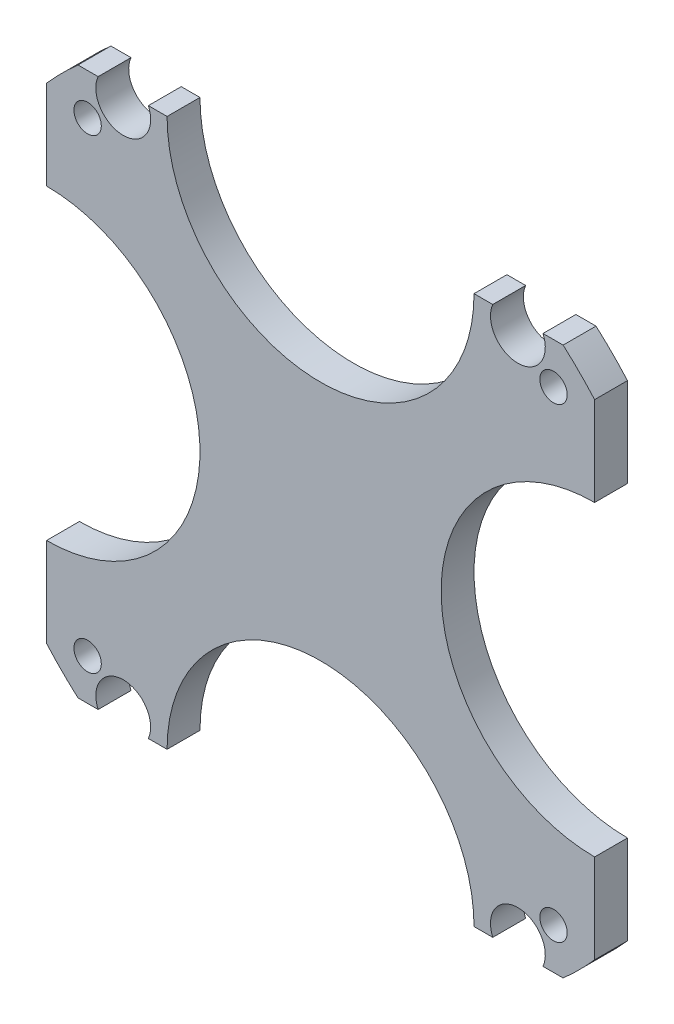
SolidWorks part; units mm, degrees
ref_plane "前视基准面" through (0, 0, 0) normal (0, 0, 1) x (1, 0, 0)
ref_plane "上视基准面" through (0, 0, 0) normal (0, 1, 0) x (1, 0, 0)
ref_plane "右视基准面" through (0, 0, 0) normal (1, 0, 0) x (0, 0, -1)
sketch "草图1" plane through (0, 0, 0) normal (0, 0, 1) x (1, 0, 0)
  line L0 (55, 0) -> (-55, 0) construction
  line L1 (-25, 25) -> (25, 25)
  line L2 (-25, 25) -> (-25, -25)
  line L3 (-25, -25) -> (25, -25)
  line L4 (25, 25) -> (25, -25)
  line L5 (-25, 25) -> (25, -25) construction
  line L6 (-25, -25) -> (25, 25) construction
  line L7 (0, -55) -> (0, 55) construction
  circle A0 centre (-21.25, 21.25) radius 1.25
  circle A1 centre (-21.25, -21.25) radius 1.25
  circle A2 centre (21.25, -21.25) radius 1.25
  circle A3 centre (21.25, 21.25) radius 1.25
  circle A4 centre (0, 0) radius 33.386
  circle A5 centre (-25, 0) radius 14
  circle A6 centre (0, 25) radius 14
  circle A7 centre (25, 0) radius 14
  circle A8 centre (0, -25) radius 14
  point P0 (0, 0)
  dimension "D3" = 2.5
  dimension "D4" = 21.25
  dimension "D5" = 28
  dimension "D1" = 50
  dimension "D2" = 50
extrude "凸台-拉伸1" add sketch "草图1" along normal blind 3 contours L3 A8 A4 L4 A7 L1 A6 L2 A5 A1 A0 A2 A3
sketch "草图2" plane through (0, 0, 3) normal (0, 0, 1) x (1, 0, 0)
  line L0 (0, -1.65) -> (0, 1.65) construction
  line L1 (18, 20) -> (-18, 20)
  line L2 (18, 20) -> (18, -20)
  line L3 (18, -20) -> (-18, -20)
  line L4 (-18, 20) -> (-18, -20)
  line L5 (18, 20) -> (-18, -20) construction
  line L6 (18, -20) -> (-18, 20) construction
  line L7 (1.65, 0) -> (-1.65, 0) construction
  circle A0 centre (-18, 24) radius 2.5
  circle A1 centre (0, 0) radius 23.8956
  arc A2 (-11, 0) -> (-25, -14) centre (-25, 0) ccw
  arc A3 (-25, -14) -> (-25, 14) centre (-25, 0) ccw construction
  circle A4 centre (-25, 0) radius 14
  circle A5 centre (25, 0) radius 14
  circle A6 centre (0, -25) radius 14
  circle A7 centre (0, 25) radius 14
  circle A8 centre (-18, -24) radius 2.5
  circle A9 centre (18, -24) radius 2.5
  circle A10 centre (18, 24) radius 2.5
  point P2 (0, 0)
  line M15 (14, -25) -> (22.1275, -25)
  line M21 (22.1275, 25) -> (14, 25)
  dimension "D1" = 5
  dimension "D3" = 18
  dimension "D2" = 24
  dimension "D4" = 36
  dimension "D5" = 40
extrude "切除-拉伸1" cut sketch "草图2" against normal blind 12 contours A10 M21 | A9 M15 | A0 | A8
